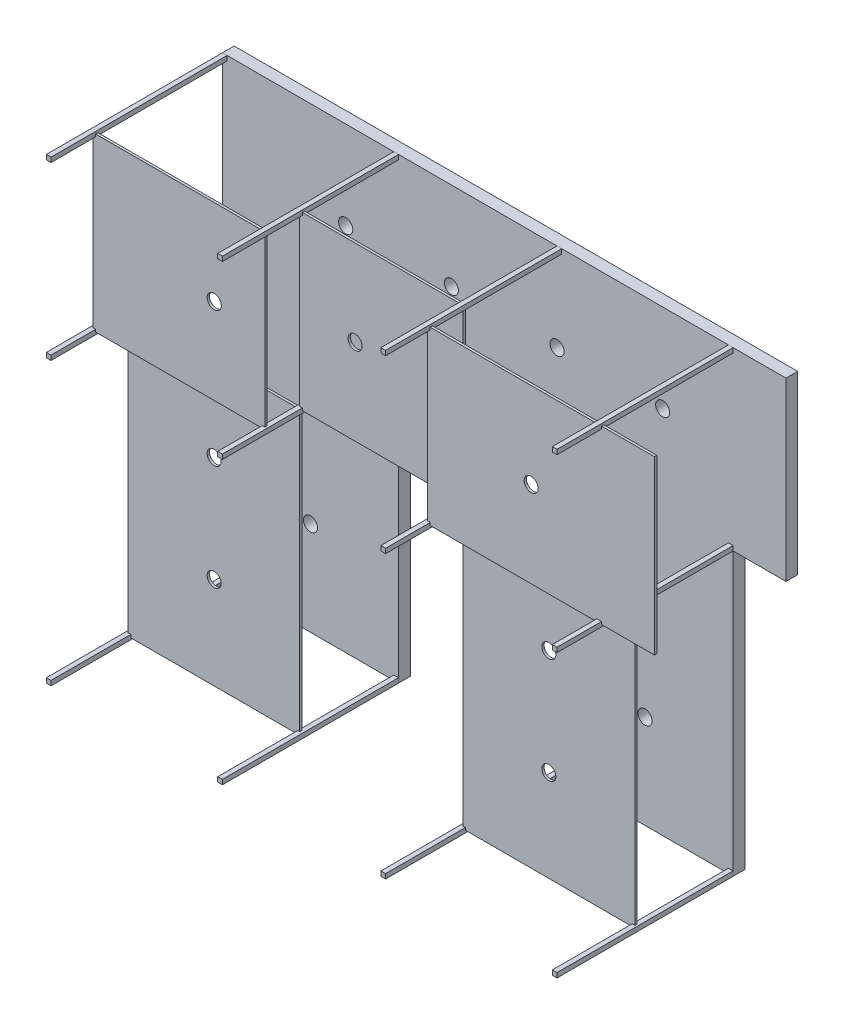
SolidWorks part; units mm, degrees
ref_plane "Front Plane" through (0, 0, 0) normal (0, 0, 1) x (1, 0, 0)
ref_plane "Top Plane" through (0, 0, 0) normal (0, 1, 0) x (1, 0, 0)
ref_plane "Right Plane" through (0, 0, 0) normal (1, 0, 0) x (0, 0, -1)
sketch "Sketch1" plane through (0, 0, 0) normal (0, 0, 1) x (1, 0, 0)
  line L0 (0, 0) -> (0, 3900)
  line L1 (0, 3900) -> (4800, 3900)
  line L2 (4800, 3900) -> (4800, 2400)
  line L3 (4800, 2400) -> (4350, 2400)
  line L4 (4350, 2400) -> (4350, 0)
  line L5 (4350, 0) -> (2850, 0)
  line L6 (2850, 0) -> (2850, 2400)
  line L7 (2850, 2400) -> (1500, 2400)
  line L8 (1500, 2400) -> (1500, 0)
  line L9 (1500, 0) -> (0, 0)
  circle A0 centre (1050, 3150) radius 60
  circle A1 centre (1950, 3150) radius 60
  circle A2 centre (2850, 3150) radius 60
  circle A3 centre (750, 800) radius 60
  circle A4 centre (3600, 800) radius 60
  circle A5 centre (3600, 1700) radius 60
  circle A6 centre (750, 1700) radius 60
  circle A7 centre (3750, 3150) radius 60
  circle A8 centre (750, 2600) radius 60
  circle A9 centre (3600, 2600) radius 60
  dimension "D8" = 1050
  dimension "D10" = 900
  dimension "D7" = 120
  dimension "D11" = 800
  dimension "D12" = 750
  dimension "D15" = 750
  dimension "D1" = 2400
  dimension "D2" = 3900
  dimension "D3" = 1350
  dimension "D4" = 1500
  dimension "D5" = 1500
  dimension "D6" = 4800
  dimension "D9" = 4
  dimension "D13" = 2
  dimension "D14" = 3
extrude "Boss-Extrude1" add sketch "Sketch1" along normal blind 100
sketch "Sketch2" plane through (0, 0, 100) normal (0, 0, 1) x (1, 0, 0)
  line L0 (2890, 2400) -> (2850, 2400)
  line L1 (0, 3900) -> (40, 3900)
  line L2 (0, 3900) -> (0, 3860)
  line L3 (0, 3860) -> (40, 3860)
  line L4 (40, 3900) -> (40, 3860)
  line L5 (0, 0) -> (40, 0)
  line L6 (0, 0) -> (0, 40)
  line L7 (0, 40) -> (40, 40)
  line L8 (40, 0) -> (40, 40)
  line L9 (1500, 0) -> (1460, 0)
  line L10 (1500, 0) -> (1500, 40)
  line L11 (1500, 40) -> (1460, 40)
  line L12 (1460, 0) -> (1460, 40)
  line L13 (1500, 2400) -> (1460, 2400)
  line L14 (1500, 2400) -> (1500, 2440)
  line L15 (1500, 2440) -> (1460, 2440)
  line L16 (1460, 2400) -> (1460, 2440)
  line L17 (2890, 2400) -> (2890, 2440)
  line L18 (2890, 2440) -> (2850, 2440)
  line L19 (2850, 2400) -> (2850, 2440)
  line L20 (1500, 3860) -> (1460, 3860)
  line L21 (4350, 0) -> (4310, 0)
  line L22 (4350, 0) -> (4350, 40)
  line L23 (4350, 40) -> (4310, 40)
  line L24 (4310, 0) -> (4310, 40)
  line L25 (2890, 0) -> (2850, 0)
  line L26 (2890, 0) -> (2890, 40)
  line L27 (2890, 40) -> (2850, 40)
  line L28 (2850, 0) -> (2850, 40)
  line L29 (4350, 2400) -> (4310, 2400)
  line L30 (4350, 2400) -> (4350, 2440)
  line L31 (4350, 2440) -> (4310, 2440)
  line L32 (4310, 2400) -> (4310, 2440)
  line L33 (4350, 3860) -> (4310, 3860)
  line L34 (4350, 3860) -> (4350, 3900)
  line L35 (4350, 3900) -> (4310, 3900)
  line L36 (4310, 3860) -> (4310, 3900)
  line L37 (2850, 0) -> (4350, 0) construction
  line L38 (2850, 2400) -> (2850, 0) construction
  line L39 (1500, 2400) -> (2850, 2400) construction
  line L40 (2890, 3860) -> (2850, 3860)
  line L41 (2890, 3860) -> (2890, 3900)
  line L42 (2890, 3900) -> (2850, 3900)
  line L43 (2850, 3860) -> (2850, 3900)
  line L44 (40, 2400) -> (0, 2400)
  line L45 (40, 2400) -> (40, 2440)
  line L46 (40, 2440) -> (0, 2440)
  line L47 (0, 2400) -> (0, 2440)
  line L48 (0, 3900) -> (0, 0) construction
  line L49 (4800, 3900) -> (0, 3900) construction
  line L50 (4350, 2400) -> (4800, 2400) construction
  line L51 (1500, 3860) -> (1500, 3900)
  line L52 (1500, 3900) -> (1460, 3900)
  line L53 (1460, 3860) -> (1460, 3900)
  line M7 (0, 0) -> (1500, 0)
  line M8 (1500, 0) -> (1500, 2400)
  line M9 (1500, 2400) -> (2850, 2400)
  line M10 (2850, 2400) -> (2850, 0)
  line M11 (2850, 0) -> (4350, 0)
  line M12 (4350, 0) -> (4350, 2400)
  line M15 (4800, 3900) -> (0, 3900)
  line M16 (0, 3900) -> (0, 0)
  dimension "D1" = 40
  dimension "D2" = 40
  dimension "D3" = 40
  dimension "D4" = 40
  dimension "D5" = 40
  dimension "D6" = 40
  dimension "D7" = 40
  dimension "D8" = 40
  dimension "D9" = 40
  dimension "D10" = 40
  dimension "D11" = 40
  dimension "D12" = 40
  dimension "D13" = 40
  dimension "D14" = 40
  dimension "D15" = 40
  dimension "D16" = 40
  dimension "D17" = 40
  dimension "D18" = 40
  dimension "D19" = 40
  dimension "D20" = 40
  dimension "D21" = 40
  dimension "D22" = 40
  dimension "D23" = 40
  dimension "D24" = 40
extrude "Boss-Extrude2" add sketch "Sketch2" along normal blind 1500 separate body contours L8 L7 M7 M16 | L16 L13 L14 L15 | L12 L11 M7 M8 | L24 L23 M11 M12 | L32 L29 L30 L31 | L36 L33 L34 M15 | L43 L40 L41 M15 | L19 L17 L18 M9 | L4 L3 M15 M16 | L45 L46 L44 M16 | L26 L27 M10 M11 | L53 L20 L51 M15
ref_plane "Plane2" through (0, 0, 900) normal (0, 0, 1) x (1, 0, 0)
sketch "Sketch3" plane through (0, 0, 900) normal (0, 0, 1) x (1, 0, 0)
  line L3 (2870.5919, 2420.0495) -> (1477.2184, 2420.0495)
  line L4 (2870.5919, 2420.0495) -> (2870.5919, 3882.092)
  line L7 (2870.5919, 3882.092) -> (1477.2184, 3882.092)
  line L8 (1477.2184, 2420.0495) -> (1477.2184, 3882.092)
  line L10 (1477.2184, 2420.0495) -> (17.0762, 2420.0495)
  line L13 (4332.9146, 2420.0495) -> (2870.5919, 2420.0495)
  line L14 (4332.9146, 2420.0495) -> (4332.9146, 20)
  line L15 (4332.9146, 20) -> (2870.5919, 20)
  line L16 (2870.5919, 2420.0495) -> (2870.5919, 20)
  line L21 (1477.2184, 2420.0495) -> (1477.2184, 13.9602)
  line L22 (1477.2184, 13.9602) -> (17.0762, 13.9602)
  line L23 (17.0762, 2420.0495) -> (17.0762, 13.9602)
ref_plane "Plane3" through (0, 0, 1200) normal (0, 0, 1) x (1, 0, 0)
sketch "Sketch5" plane through (0, 0, 1200) normal (0, 0, 1) x (1, 0, 0)
  line L0 (4800, 2400) -> (4800, 3900) construction
  line L1 (1481.2655, 2420) -> (16.3508, 2420)
  line L2 (1481.2655, 2420) -> (1481.2655, 3880.6022)
  line L3 (1481.2655, 3880.6022) -> (16.3508, 3880.6022)
  line L4 (16.3508, 2420) -> (16.3508, 3880.6022)
  line L7 (4800, 2417.6303) -> (2868.745, 2417.6303)
  line L8 (4800, 2417.6303) -> (4800, 3880.6022)
  line L9 (4800, 3880.6022) -> (2868.745, 3880.6022)
  line L10 (2868.745, 2417.6303) -> (2868.745, 3880.6022)
extrude "Boss-Extrude5" add sketch "Sketch5" along normal blind 20
extrude "Boss-Extrude6" add sketch "Sketch3" along normal blind 20 contours L10 L23 L22 L21 | L8 L3 L4 L7 | L16 L15 L14 L13
sketch "Sketch6" plane through (0, 0, 0) normal (0, 0, -1) x (-1, 0, 0)
  circle A0 centre (-3750, 3150) radius 60
  circle A2 centre (-1050, 3150) radius 60.3791
  circle A4 centre (-750, 1700) radius 60
  circle A5 centre (-750, 800) radius 60
  circle A6 centre (-3600, 800) radius 60
  circle A7 centre (-3600, 1700) radius 60
  circle A10 centre (-1950, 3150) radius 60
extrude "Cut-Extrude2" cut sketch "Sketch6" against normal through all
equation "\"A\"= 40"
equation "\"D9@Sketch2\"=\"A\""
equation "\"D10@Sketch2\"=\"A\""
equation "\"D11@Sketch2\"=\"A\""
equation "\"D12@Sketch2\"=\"A\""
equation "\"D6@Sketch2\"=\"A\""
equation "\"D5@Sketch2\"=\"A\""
equation "\"D4@Sketch2\"=\"A\""
equation "\"D3@Sketch2\"=\"A\""
equation "\"D8@Sketch2\"=\"A\""
equation "\"D7@Sketch2\"=\"A\""
equation "\"D2@Sketch2\"=\"A\""
equation "\"D1@Sketch2\"=\"A\""
equation "\"D13@Sketch2\"=\"A\""
equation "\"D14@Sketch2\"=\"A\""
equation "\"D15@Sketch2\"=\"A\""
equation "\"D16@Sketch2\"=\"A\""
equation "\"D17@Sketch2\"=\"A\""
equation "\"D18@Sketch2\"=\"A\""
equation "\"D\"= 120"
equation "\"D20@Sketch2\" = \"A\""
equation "\"D21@Sketch2\"=\"A\""
equation "\"D22@Sketch2\"=\"A\""
equation "\"D23@Sketch2\"=\"A\""
equation "\"b\"=750"
equation "\"D12@Sketch1\"=\"b\""
